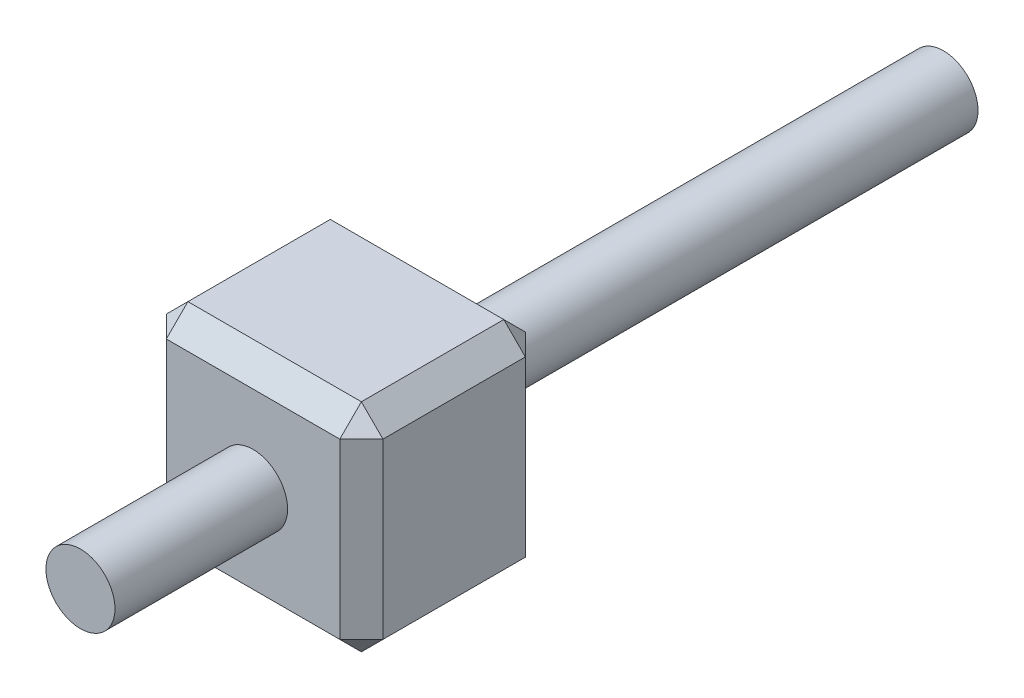
SolidWorks part; units mm, degrees
ref_plane "Face" through (0, 0, 0) normal (0, 0, 1) x (1, 0, 0)
ref_plane "Dessus" through (0, 0, 0) normal (0, 1, 0) x (1, 0, 0)
ref_plane "Droite" through (0, 0, 0) normal (1, 0, 0) x (0, 0, -1)
sketch "Esquisse1" plane through (0, 0, 0) normal (0, 0, 1) x (1, 0, 0)
  line L0 (-29.2454, 24.3197) -> (-29.2454, 21.8097) construction
  line L1 (-30.5004, 24.3197) -> (-27.9904, 24.3197)
  line L2 (-30.5004, 24.3197) -> (-30.5004, 21.8097)
  line L3 (-30.5004, 21.8097) -> (-27.9904, 21.8097)
  line L4 (-27.9904, 24.3197) -> (-27.9904, 21.8097)
  dimension "D1" = 2.51
  dimension "D2" = 2.51
extrude "Extrusion1" add sketch "Esquisse1" along normal blind 2.15
sketch "Esquisse2" plane through (0, 0, 2.15) normal (0, 0, 1) x (1, 0, 0)
  line L0 (-29.2454, 24.3197) -> (-29.2454, 21.8097) construction
  line L1 (-27.9904, 24.3197) -> (-30.5004, 24.3197) construction
  line L2 (-30.5004, 21.8097) -> (-27.9904, 21.8097) construction
  circle A0 centre (-29.2454, 23.0647) radius 0.4
  dimension "D1" = 0.8
extrude "Extrusion2" add sketch "Esquisse2" along normal blind 2 and the other way blind 8
chamfer "Chanfrein1" distance 0.25 angle 45 12 edges at (-27.9904, 23.0647, 2.15) (-29.2454, 24.3197, 2.15) (-30.5004, 23.0647, 2.15) (-29.2454, 24.3197, 0) (-27.9904, 23.0647, 0) (-29.2454, 21.8097, 0) (-30.5004, 23.0647, 0) (-29.2454, 21.8097, 2.15) (-30.5004, 24.3197, 1.075) (-27.9904, 24.3197, 1.075) (-27.9904, 21.8097, 1.075) (-30.5004, 21.8097, 1.075)
